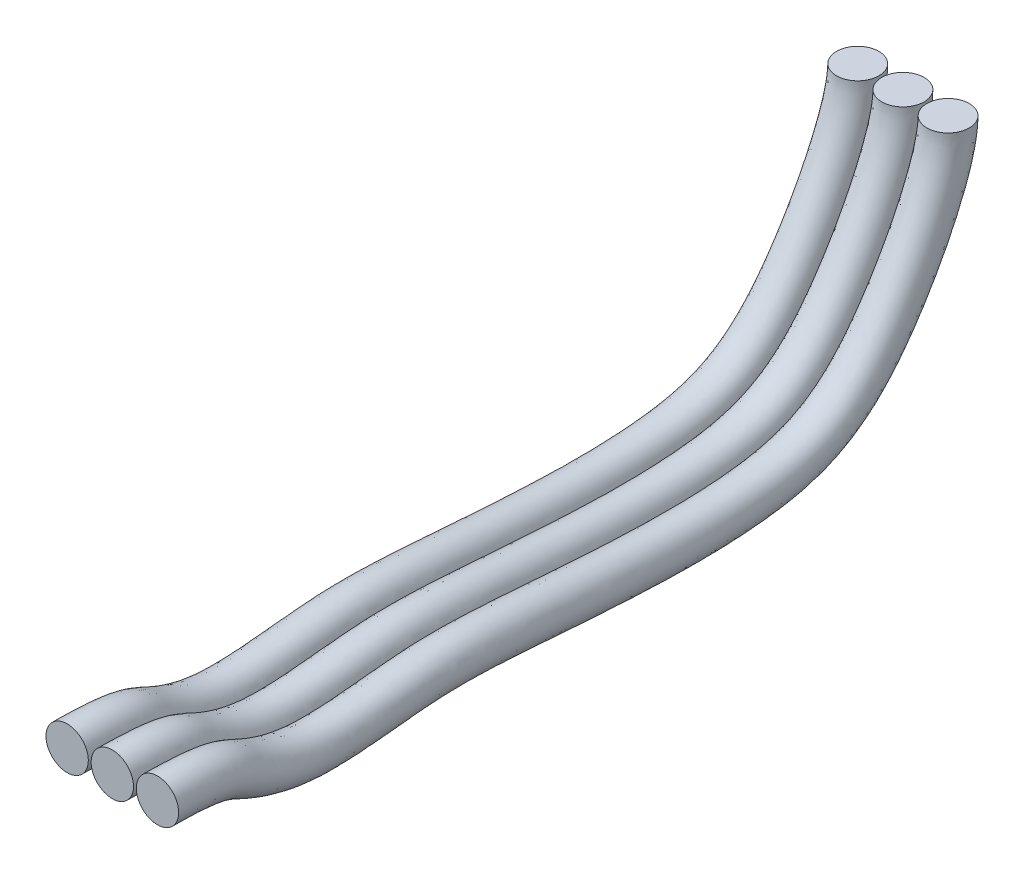
SolidWorks part; units mm, degrees
ref_plane "Front Plane" through (0, 0, 0) normal (0, 0, 1) x (1, 0, 0)
ref_plane "Top Plane" through (0, 0, 0) normal (0, 1, 0) x (1, 0, 0)
ref_plane "Right Plane" through (0, 0, 0) normal (1, 0, 0) x (0, 0, -1)
sketch "Sketch2" plane through (0, 0, 0) normal (1, 0, 0) x (0, 0, -1)
  line L0 (0, 0) -> (28, 0) construction
  line L1 (28, 0) -> (28, 7) construction
  line L2 (28, 15.0245) -> (28, 12.9755) construction
  line L3 (1.6002, 0) -> (-1.6005, 0) construction
  spline S0 degree 3 poles (0, 0) (2.0004, 0) (2.7629, -0.502) (5.1128, -1.3164) (9.4195, -0.6919) (12.3437, -0.8311) (21.6551, -1.6004) (25.3828, 0.4652) (28, 5.7193) (28, 7) knots 0 0 0 0 0.131692 0.270614 0.409752 0.581041 0.755263 0.891487 1 1 1 1
  dimension "D1" = 28
  dimension "D2" = 7
sketch "Sketch3" plane through (0, 0, 0) normal (0, 0, 1) x (1, 0, 0)
  circle A0 centre (0, 0) radius 0.75
  circle A1 centre (1.6, 0) radius 0.75
  circle A2 centre (-1.6, 0) radius 0.75
  dimension "D1" = 1.5
  dimension "D2" = 1.5
  dimension "D3" = 1.5
  dimension "D4" = 1.6
  dimension "D5" = 1.6
sweep "Sweep1" add profiles "Sketch3" path "Sketch2"
